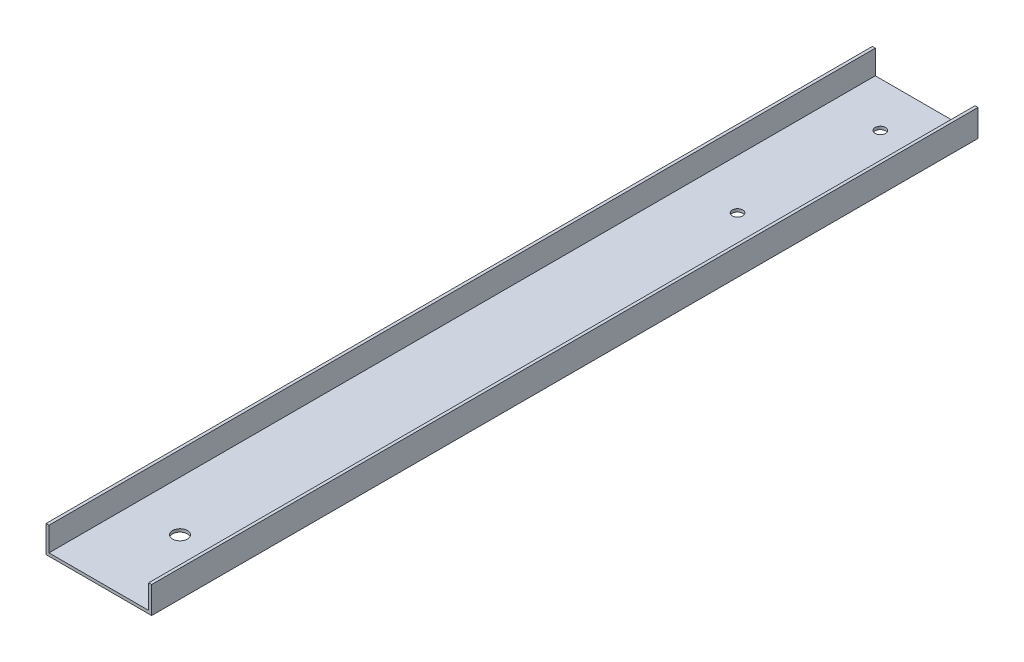
SolidWorks part; units mm, degrees
material "1023 Carbon Steel Sheet (SS)"
ref_plane "Front Plane" through (0, 0, 0) normal (0, 0, 1) x (1, 0, 0)
ref_plane "Top Plane" through (0, 0, 0) normal (0, 1, 0) x (1, 0, 0)
ref_plane "Right Plane" through (0, 0, 0) normal (1, 0, 0) x (0, 0, -1)
sketch "Sketch1" plane through (0, 0, 0) normal (0, 0, 1) x (1, 0, 0)
  line L0 (0, 0) -> (0, -11.5316)
  line L1 (0, -11.5316) -> (45.2628, -11.5316)
  line L2 (45.2628, -11.5316) -> (45.2628, 0)
  line L3 (45.2628, 0) -> (43.9928, 0)
  line L4 (43.9928, 0) -> (43.9928, -10.2616)
  line L5 (43.9928, -10.2616) -> (1.27, -10.2616)
  line L6 (1.27, -10.2616) -> (1.27, 0)
  line L7 (1.27, 0) -> (0, 0)
  dimension "D1" = 45.2628
  dimension "D2" = 11.5316
  dimension "D3" = 1.27
  dimension "D4" = 1.27
  dimension "D5" = 1.27
extrude "Boss-Extrude1" add sketch "Sketch1" along normal blind 354.0125
sketch "Sketch2" plane through (0, -11.5316, 0) normal (0, -1, 0) x (-1, 0, 0)
  line L0 (-22.6314, 0) -> (-22.6314, -354.0125) construction
  line L1 (0, 0) -> (-45.2628, 0) construction
  line L2 (0, -354.0125) -> (-45.2628, -354.0125) construction
  circle A0 centre (-22.6314, -19.1897) radius 2.2225
  circle A1 centre (-22.6314, -80.391) radius 2.2225
  circle A2 centre (-22.6314, -319.2145) radius 3.175
  dimension "D2" = 4.445
  dimension "D5" = 6.35
  dimension "D1" = 19.1897
  dimension "D3" = 80.391
  dimension "D4" = 34.798
extrude "Cut-Extrude1" cut sketch "Sketch2" against normal blind 1.27
ref_plane "Center plane" through (22.6314, 0, 0) normal (1, 0, 0) x (0, 0, -1)
